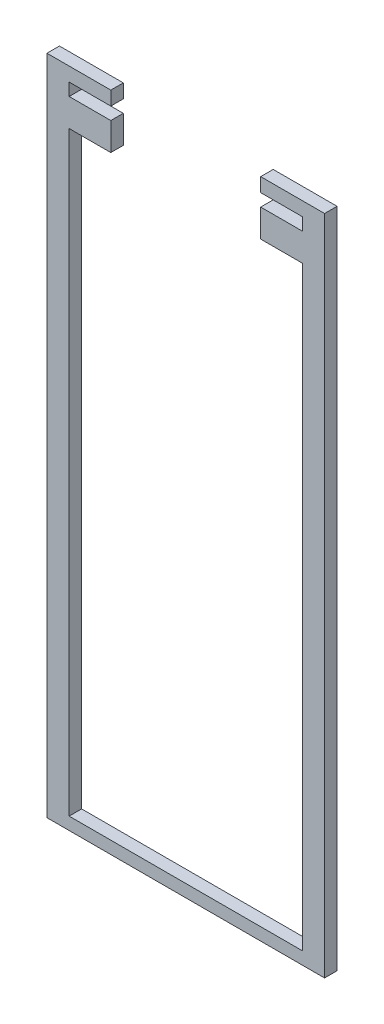
SolidWorks part; units mm, degrees
material "Teak"
ref_plane "Front Plane" through (0, 0, 0) normal (0, 0, 1) x (1, 0, 0)
ref_plane "Top Plane" through (0, 0, 0) normal (0, 1, 0) x (1, 0, 0)
ref_plane "Right Plane" through (0, 0, 0) normal (1, 0, 0) x (0, 0, -1)
sketch "Sketch1" plane through (0, 0, 0) normal (0, 0, 1) x (1, 0, 0)
  line L0 (48.1209, 127.3926) -> (48.1209, -111.1074) construction
  line L1 (-51.8791, 127.3926) -> (-51.8791, -111.1074) construction
  line L2 (-51.8791, -111.1074) -> (48.1209, -111.1074) construction
  line L3 (40.1209, 107.8926) -> (40.1209, -106.6074) construction
  line L4 (-43.8791, 107.8926) -> (-43.8791, -101.1074) construction
  line L5 (40.1209, -106.6074) -> (-43.8791, -106.6074) construction
  line L6 (-43.8791, -106.6074) -> (-43.8791, -101.1074) construction
  line L7 (-43.8791, 117.8926) -> (-28.8791, 117.8926) construction
  line L8 (-28.8791, 117.8926) -> (-28.8791, 107.8926) construction
  line L9 (-28.8791, 107.8926) -> (-43.8791, 107.8926) construction
  line L10 (-43.8791, 117.8926) -> (-43.8791, 122.3926) construction
  line L11 (-43.8791, 122.3926) -> (-28.8791, 122.3926) construction
  line L12 (-28.8791, 122.3926) -> (-28.8791, 127.3926) construction
  line L13 (-28.8791, 127.3926) -> (-51.8791, 127.3926) construction
  line L14 (40.1209, 117.8926) -> (25.1209, 117.8926) construction
  line L15 (25.1209, 117.8926) -> (25.1209, 107.8926) construction
  line L16 (25.1209, 107.8926) -> (40.1209, 107.8926) construction
  line L17 (40.1209, 117.8926) -> (40.1209, 122.3926) construction
  line L18 (40.1209, 122.3926) -> (25.1209, 122.3926) construction
  line L19 (25.1209, 122.3926) -> (25.1209, 127.3926) construction
  line L20 (25.1209, 127.3926) -> (48.1209, 127.3926) construction
sketch "Sketch2" plane through (0, 0, 0) normal (0, 0, 1) x (1, 0, 0)
  line L0 (40.1209, 117.8926) -> (40.1209, 122.3926) construction
  line L1 (25.1209, 127.3926) -> (48.1209, 127.3926) construction
  line L2 (25.1209, 122.3926) -> (25.1209, 127.3926) construction
  line L3 (40.1209, 122.3926) -> (25.1209, 122.3926) construction
  line L4 (40.1209, 117.8926) -> (25.1209, 117.8926) construction
  line L5 (25.1209, 117.8926) -> (25.1209, 107.8926) construction
  line L6 (25.1209, 107.8926) -> (40.1209, 107.8926) construction
  line L7 (-28.8791, 107.8926) -> (-43.8791, 107.8926) construction
  line L8 (-28.8791, 117.8926) -> (-28.8791, 107.8926) construction
  line L9 (-43.8791, 117.8926) -> (-28.8791, 117.8926) construction
  line L10 (-43.8791, 117.8926) -> (-43.8791, 122.3926) construction
  line L11 (-43.8791, 122.3926) -> (-28.8791, 122.3926) construction
  line L12 (-28.8791, 122.3926) -> (-28.8791, 127.3926) construction
  line L13 (-28.8791, 127.3926) -> (-51.8791, 127.3926) construction
  line L14 (40.1209, -106.6074) -> (-43.8791, -106.6074) construction
  line L15 (-51.8791, -111.1074) -> (48.1209, -111.1074) construction
  line L16 (48.1209, 127.3926) -> (48.1209, -111.1074) construction
  line L17 (40.1209, 107.8926) -> (40.1209, -106.6074) construction
  line L18 (-51.8791, 127.3926) -> (-51.8791, -111.1074) construction
  line L19 (40.1209, 117.8926) -> (40.1209, 122.3926)
  line L20 (25.1209, 127.3926) -> (48.1209, 127.3926)
  line L21 (25.1209, 122.3926) -> (25.1209, 127.3926)
  line L22 (40.1209, 122.3926) -> (25.1209, 122.3926)
  line L23 (40.1209, 117.8926) -> (25.1209, 117.8926)
  line L24 (25.1209, 117.8926) -> (25.1209, 107.8926)
  line L25 (25.1209, 107.8926) -> (40.1209, 107.8926)
  line L26 (-28.8791, 107.8926) -> (-43.8791, 107.8926)
  line L27 (-28.8791, 117.8926) -> (-28.8791, 107.8926)
  line L28 (-43.8791, 117.8926) -> (-28.8791, 117.8926)
  line L29 (-43.8791, 117.8926) -> (-43.8791, 122.3926)
  line L30 (-43.8791, 122.3926) -> (-28.8791, 122.3926)
  line L31 (-28.8791, 122.3926) -> (-28.8791, 127.3926)
  line L32 (-28.8791, 127.3926) -> (-51.8791, 127.3926)
  line L33 (40.1209, -106.6074) -> (-43.8791, -106.6074)
  line L34 (-51.8791, -111.1074) -> (48.1209, -111.1074)
  line L35 (48.1209, 127.3926) -> (48.1209, -111.1074)
  line L36 (40.1209, 107.8926) -> (40.1209, -106.6074)
  line L37 (-51.8791, 127.3926) -> (-51.8791, -111.1074)
  line L38 (-43.8791, -106.6074) -> (-43.8791, 107.8926)
extrude "Boss-Extrude1" add sketch "Sketch2" along normal blind 4.5
